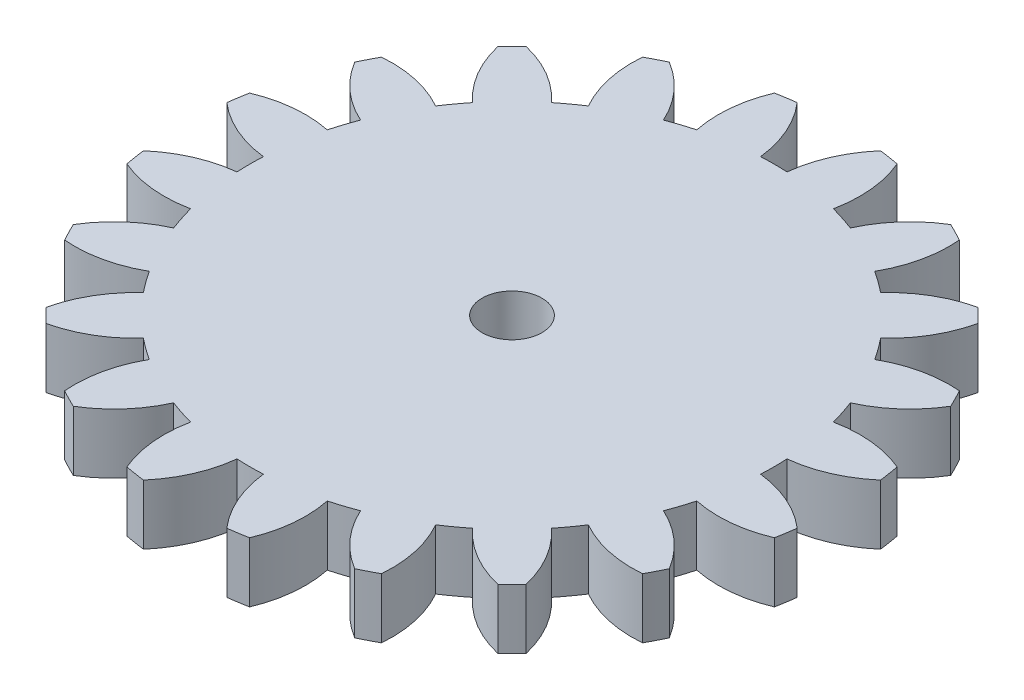
SolidWorks part; units mm, degrees
ref_plane "Front Plane" through (0, 0, 0) normal (0, 0, 1) x (1, 0, 0)
ref_plane "Top Plane" through (0, 0, 0) normal (0, 1, 0) x (1, 0, 0)
ref_plane "Right Plane" through (0, 0, 0) normal (1, 0, 0) x (0, 0, -1)
sketch "Sketch1" plane through (0, 0, 0) normal (0, 1, 0) x (1, 0, 0)
  circle A0 centre (0, 0) radius 16.5
  dimension "addendumDiamteter" = 33
extrude "Boss-Extrude1" add sketch "Sketch1" along normal blind 3
sketch "Sketch2" plane through (0, 3, 0) normal (0, 1, 0) x (1, 0, 0)
  line L0 (0, 0) -> (0, 28.8712) construction
  line L1 (0, 0) -> (-2.697, 17.0281) construction
  line L3 (-1.1757, 14.9539) -> (-2.3393, 14.7696) construction
  circle A0 centre (0, 0) radius 15 construction
  circle A2 centre (0, 0) radius 13.125 construction
  circle A3 centre (0, 0) radius 14.0954 construction
  arc A4 (-0.6616, 13.1083) -> (0.6616, 13.1083) centre (0, 0) cw
  arc A5 (-2.087, 16.3675) -> (2.087, 16.3675) centre (0, 0) cw
  circle A6 centre (0, 0) radius 16.5 construction
  arc A7 (-2.087, 16.3675) -> (-0.6616, 13.1083) centre (-6.6245, 12.4417) cw
  arc A8 (2.087, 16.3675) -> (0.6616, 13.1083) centre (6.6245, 12.4417) ccw
  dimension "dedendumCircle" = 26.25
  dimension "baseDiameter" = 28.1908
  dimension "PitchDiameter" = 30
  dimension "D1" = 6
  dimension "D4" = 9
  dimension "D2" = 1.1781
extrude "Cut-Extrude1" cut sketch "Sketch2" against normal through all
pattern_circular "CirPattern1" count 20 over 360 about axis through (0, 0, 0) along (0, 1, 0) of "Cut-Extrude1"
sketch "Sketch3" [suppressed] plane through (0, 3, 0) normal (0, 1, 0) x (1, 0, 0)
  line L0 (0, 2) -> (-4.1557, 9.9831)
  line L2 (4.1557, 9.9831) -> (0, 2)
  line L3 (0, 0) -> (0, 31.2074) construction
  line L4 (0, 0) -> (46.4667, 0) construction
  line L5 (-4.1557, 9.9831) -> (4.1557, 9.9831) construction
  arc A0 (-4.1557, 9.9831) -> (4.1557, 9.9831) centre (0, -1.2743) cw
  dimension "D4" = 12
  dimension "D1" = 75
  dimension "D2" = 5
  dimension "D3" = 11
extrude "Cut-Extrude2" [suppressed] cut sketch "Sketch3" against normal blind 10
fillet "Fillet1" [suppressed] radius 1
fillet "Fillet2" [suppressed] radius 1
fillet "Fillet3" [suppressed] radius 1
pattern_circular "CirPattern2" [suppressed] count 6 over 360
sketch "Sketch4" plane through (0, 0, 0) normal (0, -1, 0) x (1, 0, 0)
  line L0 (-26.1838, 0) -> (42.0456, 0) construction
  line L1 (0, 35.0594) -> (0, -36.1668) construction
  circle A0 centre (0, 0) radius 1.5
  dimension "D1" = 3
  dimension "D2" = 0
extrude "Cut-Extrude3" cut sketch "Sketch4" against normal blind 10
equation "\"module\"= 1.5"
equation "\"teeth\"= 20"
equation "\"pressureAngle\"= 20deg"
equation "\"gearThickness\"= 3"
equation "\"addendumFactor\"= 1"
equation "\"dedendumFactor\"= 1.25"
equation "\"pitch\"= 1 / \"module\""
equation "\"pitchDiameter\"= \"teeth\" / \"pitch\""
equation "\"addendum\"= \"addendumFactor\" / \"pitch\""
equation "\"dedendum\"= \"dedendumFactor\" / \"pitch\""
equation "\"addendumDiamteter@Sketch1\"=\"pitchDiameter\"+(\"addendum\"*2)"
equation "\"dedendumCircle@Sketch2\"=\"pitchDiameter\" -2 *\"dedendum\""
equation "\"baseDiameter@Sketch2\"=\"pitchDiameter\"*cos( \"pressureAngle\")"
equation "\"PitchDiameter@Sketch2\"=\"pitchDiameter\""
equation "\"D4@Sketch2\"=180/\"teeth\""
equation "\"D1@Sketch2\"=\"pitchDiameter\"/5"
equation "\"D2@Sketch2\"=PI / 2 / \"pitch\" / 2"
equation "\"D1@CirPattern1\"=\"teeth\""
